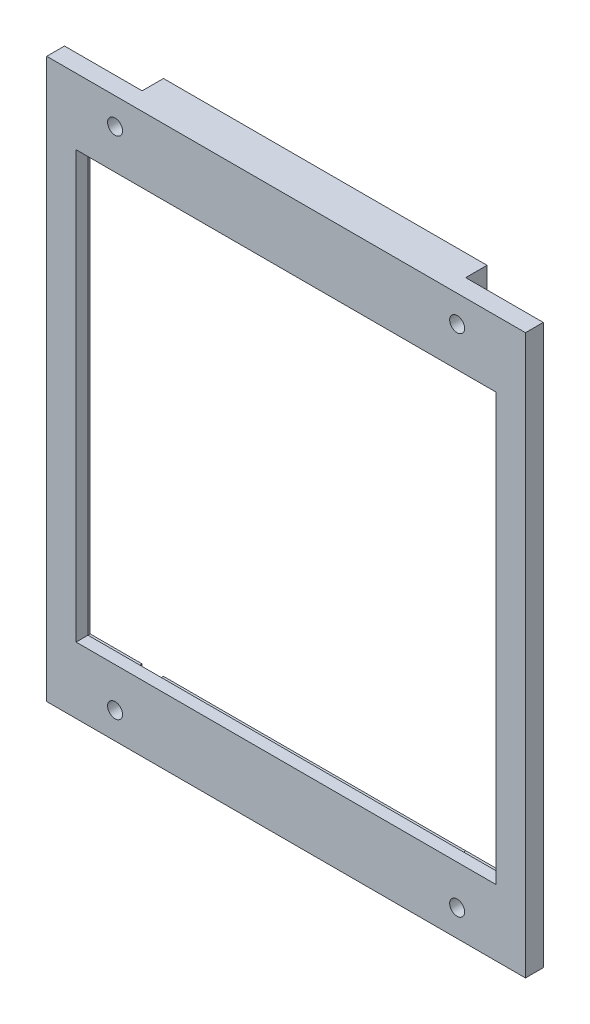
SolidWorks part; units mm, degrees
ref_plane "Front Plane" through (0, 0, 0) normal (0, 0, 1) x (1, 0, 0)
ref_plane "Top Plane" through (0, 0, 0) normal (0, 1, 0) x (1, 0, 0)
ref_plane "Right Plane" through (0, 0, 0) normal (1, 0, 0) x (0, 0, -1)
sketch "Sketch1" plane through (0, 0, 6.1) normal (0, 0, 1) x (1, 0, 0)
  line L0 (-67.25, 78.5) -> (67.25, 78.5)
  line L1 (67.25, 78.5) -> (67.25, -78.5)
  line L2 (-67.25, -78.5) -> (-67.25, 78.5)
  line L3 (-67.1, 0) -> (-59.525, 0) construction
  line L4 (67.25, 5) -> (67.25, 83.5) construction
  line L5 (74.675, 0) -> (82.25, 0) construction
  line L6 (-74.675, 0) -> (-82.25, 0) construction
  line L7 (-59, -59.9) -> (59, -59.9)
  line L8 (-67.25, -78.5) -> (67.25, -78.5)
  line L21 (59, 59.9) -> (59, 0)
  line L22 (-59, 59.9) -> (59, 59.9)
  line L23 (-59, 0) -> (-59, 59.9)
  line L24 (59, 59.9) -> (59, -59.9)
  line L25 (-59, 59.9) -> (59, 59.9)
  line L26 (-59, -59.9) -> (-59, 59.9)
  circle A0 centre (-48.05, 70.9904) radius 2.1
  circle A1 centre (48.05, 70.9904) radius 2.1
  circle A2 centre (48.05, 70.9904) radius 2.1 construction
  circle A3 centre (-48.05, 70.9904) radius 2.1 construction
  circle A4 centre (48.05, -70.9904) radius 2.1
  circle A5 centre (-48.05, -70.9904) radius 2.1
  point P28 (-67.25, 0)
  point P29 (67.25, 0)
  dimension "D1" = 1
extrude "Boss-Extrude1" add sketch "Sketch1" along normal blind 5
sketch "Sketch2" plane through (0, 0, 6.1) normal (0, 0, -1) x (-1, 0, 0)
  line L9 (-45.4729, 60.9) -> (-45.4729, 66.95)
  line L10 (-45.4729, 66.95) -> (45.475, 66.95)
  line L11 (45.475, 66.95) -> (45.475, 60.9)
  line L12 (45.475, 60.9) -> (-45.4729, 60.9)
  line L14 (-45.45, 66.925) -> (-45.425, 31.4857) construction
  line L16 (45.45, 66.925) -> (-45.45, 66.925) construction
  line L17 (-10.2, 60.925) -> (-45.4458, 60.925) construction
  line L18 (-74.675, 0) -> (-82.25, 0) construction
  line L19 (45.475, -60.9) -> (-45.4729, -60.9)
  line L20 (45.475, -66.95) -> (45.475, -60.9)
  line L21 (-45.4729, -66.95) -> (45.475, -66.95)
  line L22 (-45.4729, -60.9) -> (-45.4729, -66.95)
  point P4 (-45.4729, 63.925)
  dimension "D1" = 0.025
  dimension "D2" = 0.025
  dimension "D3" = 0.025
  dimension "D4" = 0.025
extrude "Cut-Extrude1" cut sketch "Sketch2" against normal up to surface (1.57 mm away)
sketch "Sketch3" plane through (0, 0, 0.1) normal (0, 0, 1) x (1, 0, 0)
  line L0 (-45.45, -78.5) -> (45.45, -78.5)
  line L1 (-67.25, -78.5) -> (67.25, -78.5) construction
  line L2 (-45.45, -150) -> (-45.45, -31.4857) construction
  line L3 (45.45, -31.4857) -> (45.45, -150) construction
  line L4 (45.45, -78.5) -> (45.45, -66.95)
  line L5 (45.45, -66.95) -> (-45.45, -66.95)
  line L6 (-45.45, -66.95) -> (-45.45, -78.5)
  line L7 (-45.45, -66.925) -> (45.45, -66.925) construction
  line L8 (-74.675, 0) -> (-82.25, 0) construction
  line L9 (-45.45, 66.95) -> (-45.45, 78.5)
  line L10 (45.45, 66.95) -> (-45.45, 66.95)
  line L11 (45.45, 78.5) -> (45.45, 66.95)
  line L12 (-45.45, 78.5) -> (45.45, 78.5)
  dimension "D1" = 0.025
extrude "Boss-Extrude2" add sketch "Sketch3" along normal up to surface (6 mm away) up to face at (-0.0011, 63.925, 6.1)
sketch "Sketch4" plane through (0, 0, 6.1) normal (0, 0, -1) x (-1, 0, 0)
  line L8 (-60.025, -60.925) -> (60.025, -60.925)
  line L9 (60.025, -60.925) -> (60.025, 60.925)
  line L10 (60.025, 60.925) -> (-60.025, 60.925)
  line L11 (-60.025, 60.925) -> (-60.025, -60.925)
  line L12 (-60.025, -60.925) -> (60.025, -60.925)
  line L13 (60.025, -60.925) -> (60.025, 60.925)
  line L14 (60.025, 60.925) -> (-60.025, 60.925)
  line L15 (-60.025, 60.925) -> (-60.025, -60.925)
  dimension "D1" = 1.025
extrude "Cut-Extrude2" cut sketch "Sketch4" against normal blind 1.65
